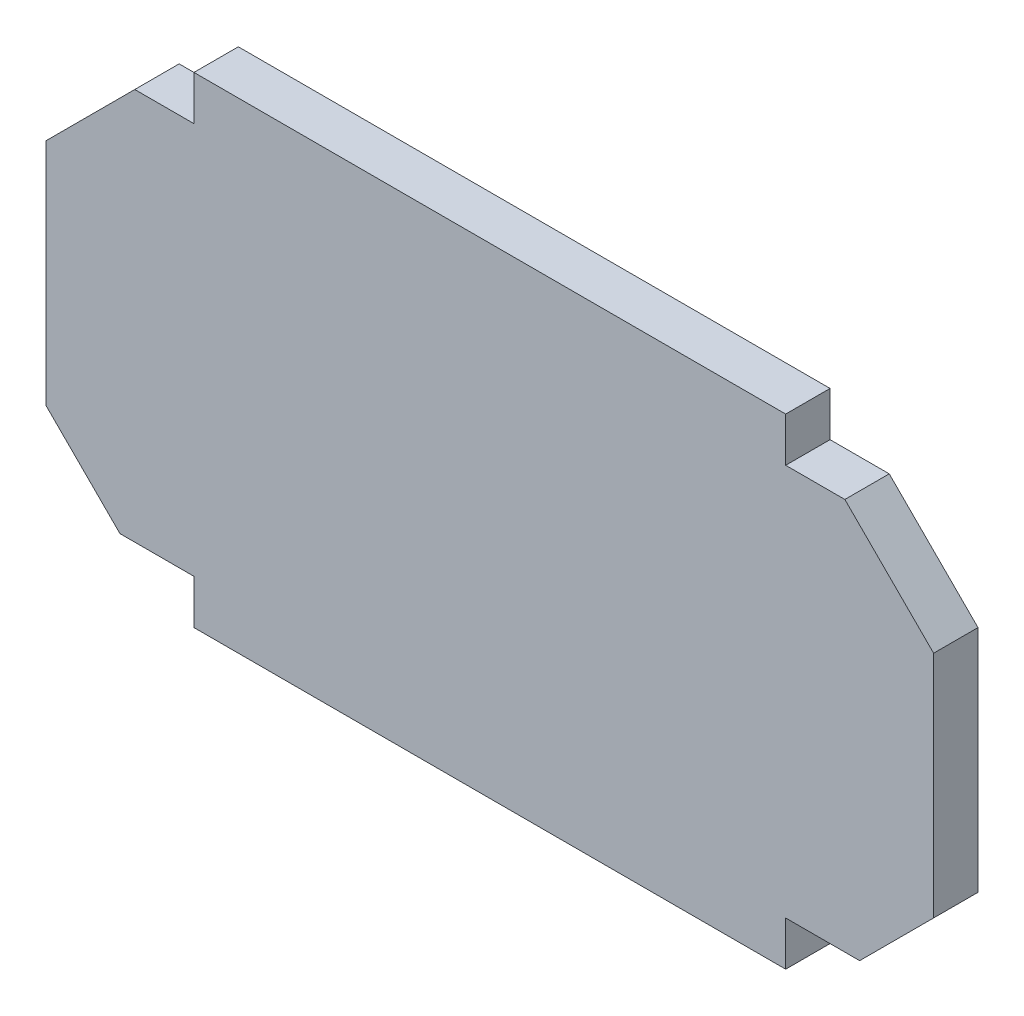
SolidWorks part; units mm, degrees
ref_plane "Front Plane" through (0, 0, 0) normal (0, 0, 1) x (1, 0, 0)
ref_plane "Top Plane" through (0, 0, 0) normal (0, 1, 0) x (1, 0, 0)
ref_plane "Right Plane" through (0, 0, 0) normal (1, 0, 0) x (0, 0, -1)
sketch "Sketch1" plane through (0, 0, 0) normal (0, 0, 1) x (1, 0, 0)
  line L0 (0, 60.5962) -> (0, -60.5962) construction
  line L2 (20, 34.5) -> (-20, 34.5)
  line L3 (-20, 34.5) -> (-20, 31.5)
  line L4 (-20, 31.5) -> (-24, 31.5)
  line L5 (-30, 25.5) -> (-30, 10)
  line L6 (-25, 5) -> (-20, 5)
  line L7 (-20, 5) -> (-20, 2)
  line L8 (-20, 2) -> (20, 2)
  line L9 (-24, 31.5) -> (-30, 25.5)
  line L10 (-30, 10) -> (-25, 5)
  line L11 (20, 5) -> (20, 2)
  line L12 (25, 5) -> (20, 5)
  line L13 (30, 10) -> (25, 5)
  line L14 (24, 31.5) -> (30, 25.5)
  line L15 (20, 34.5) -> (20, 31.5)
  line L16 (20, 31.5) -> (24, 31.5)
  line L17 (30, 25.5) -> (30, 10)
  point P0 (0, 0)
  point P4 (0, 0)
  point P8 (0, 0)
  point P11 (-30, 5)
  point P12 (-30, 31.5)
  point P21 (0, 2)
  point P27 (0, 34.5)
  dimension "D1" = 20
  dimension "D2" = 10
  dimension "D3" = 20
  dimension "D4" = 3
  dimension "D5" = 3
  dimension "D8" = 20.5
extrude "Boss-Extrude2" add sketch "Sketch1" along normal blind 3
